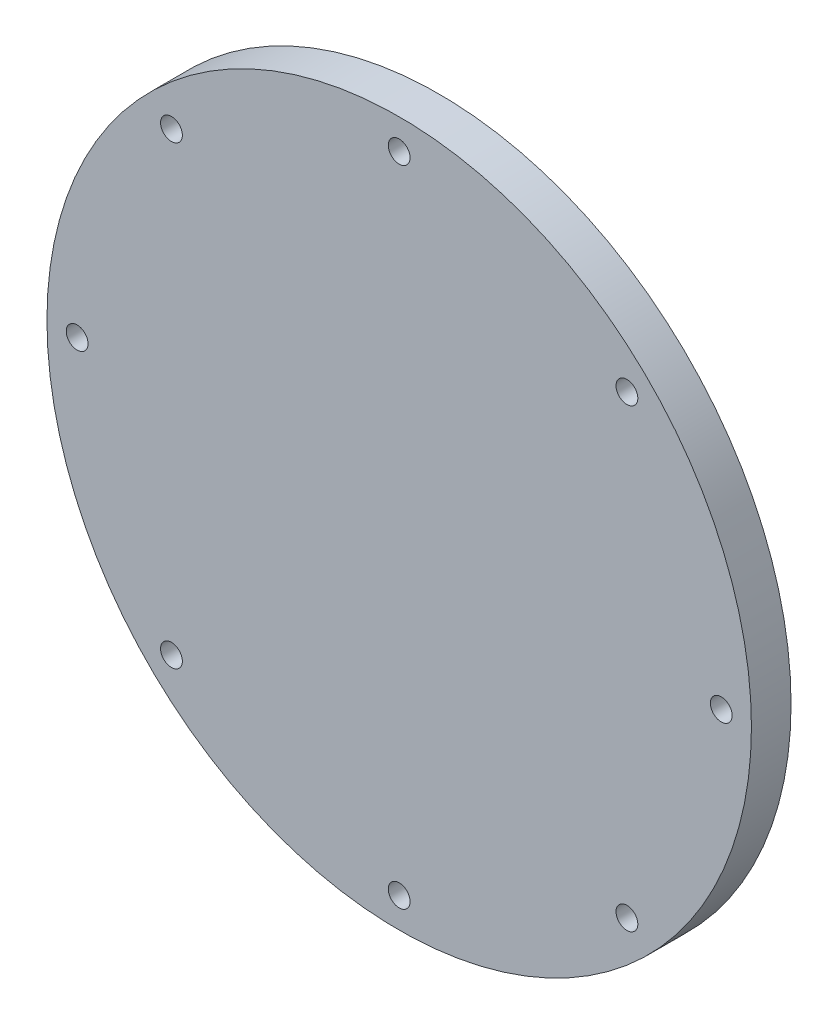
SolidWorks part; units mm, degrees
ref_plane "Front Plane" through (0, 0, 0) normal (0, 0, 1) x (1, 0, 0)
ref_plane "Top Plane" through (0, 0, 0) normal (0, 1, 0) x (1, 0, 0)
ref_plane "Right Plane" through (0, 0, 0) normal (1, 0, 0) x (0, 0, -1)
sketch "Sketch2" plane through (0, 0, 0) normal (0, 0, 1) x (1, 0, 0)
  circle A0 centre (0, 0) radius 88.9
  dimension "D1" = 177.8
extrude "Boss-Extrude1" add sketch "Sketch2" along normal blind 10
sketch "Sketch3" plane through (0, 0, 10) normal (0, 0, 1) x (1, 0, 0)
  circle A0 centre (0, 81.28) radius 2.75
  circle A1 centre (0, 0) radius 88.9 construction
  circle A2 centre (57.4736, 57.4736) radius 2.75
  circle A3 centre (81.28, 0) radius 2.75
  circle A4 centre (57.4736, -57.4736) radius 2.75
  circle A5 centre (0, -81.28) radius 2.75
  circle A6 centre (-57.4736, -57.4736) radius 2.75
  circle A7 centre (-81.28, 0) radius 2.75
  circle A8 centre (-57.4736, 57.4736) radius 2.75
  point P20 (0, 0)
  dimension "D1" = 5.5
  dimension "D2" = 81.28
  dimension "D3" = 8
extrude "Cut-Extrude1" cut sketch "Sketch3" against normal through all
